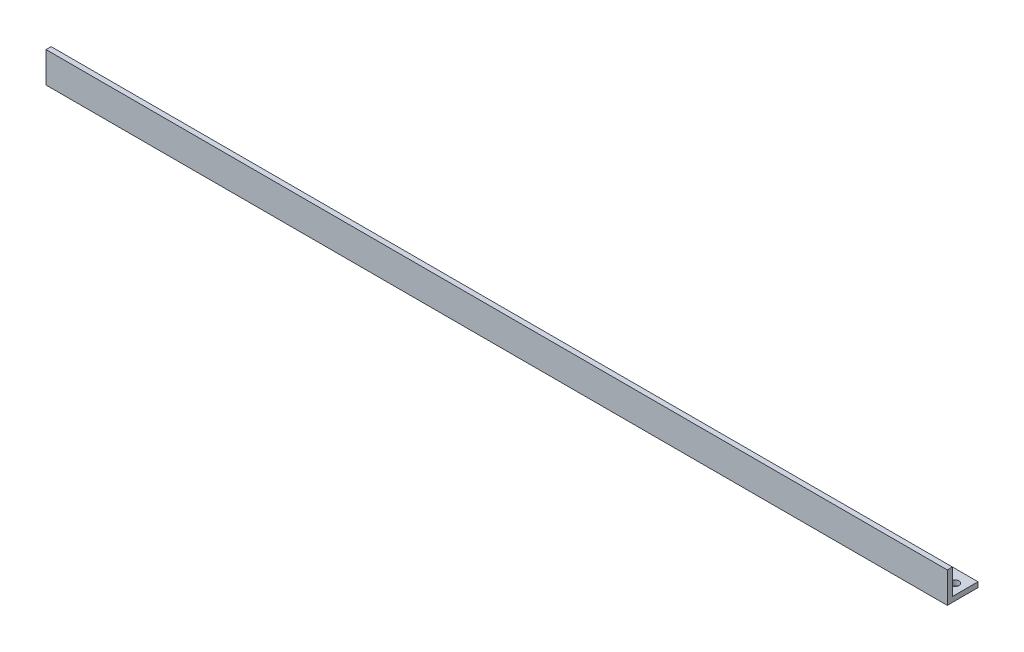
SolidWorks part; units mm, degrees
ref_plane "Front" through (0, 0, 0) normal (0, 0, 1) x (1, 0, 0)
ref_plane "Top" through (0, 0, 0) normal (0, 1, 0) x (1, 0, 0)
ref_plane "Right" through (0, 0, 0) normal (1, 0, 0) x (0, 0, -1)
sketch "Sketch1" plane through (0, 0, 0) normal (1, 0, 0) x (0, 0, -1)
  line L0 (3.175, 3.175) -> (3.175, 19.05)
  line L1 (0, 0) -> (19.05, 0)
  line L2 (0, 0) -> (0, 19.05)
  line L5 (3.175, 3.175) -> (19.05, 3.175)
  line L6 (0, 19.05) -> (3.175, 19.05)
  line L7 (19.05, 0) -> (19.05, 3.175)
  dimension "D1" = 19.05
  dimension "D2" = 3.175
extrude "Boss-Extrude1" add sketch "Sketch1" along normal blind 558.8
sketch "Sketch2" plane through (0, 3.175, 0) normal (0, 1, 0) x (1, 0, 0)
  line L0 (279.4, 19.05) -> (279.4, 3.175) construction
  line L1 (558.8, 19.05) -> (0, 19.05) construction
  line L2 (558.8, 3.175) -> (0, 3.175) construction
  line L3 (279.4, 11.1125) -> (552.45, 11.1125) construction
  line L4 (279.4, 11.1125) -> (6.35, 11.1125) construction
  circle A0 centre (552.45, 11.1125) radius 2.54
  circle A1 centre (6.35, 11.1125) radius 2.54
  dimension "D2" = 5.08
  dimension "D1" = 546.1
extrude "Cut-Extrude1" cut sketch "Sketch2" against normal up to next
